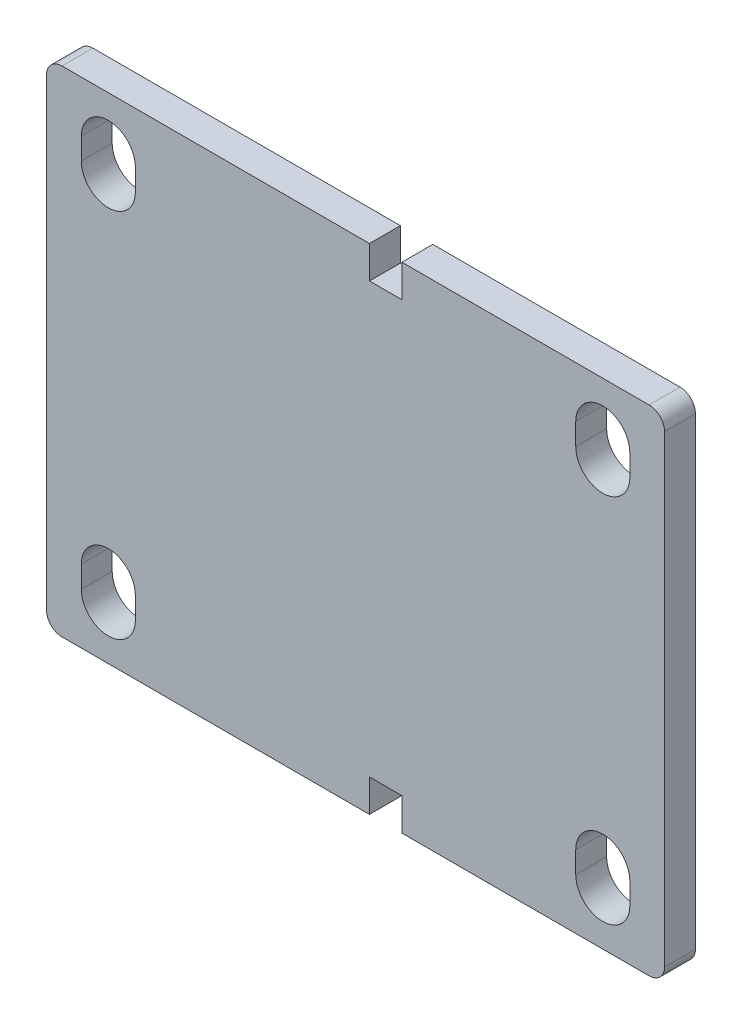
SolidWorks part; units mm, degrees
material "Acier S235"
ref_plane "Plan de face" through (0, 0, 0) normal (0, 0, 1) x (1, 0, 0)
ref_plane "Plan de dessus" through (0, 0, 0) normal (0, 1, 0) x (1, 0, 0)
ref_plane "Plan de droite" through (0, 0, 0) normal (1, 0, 0) x (0, 0, -1)
sketch "Esquisse1" plane through (0, 0, 0) normal (0, 0, 1) x (1, 0, 0)
  line L1 (100, -80) -> (-100, -80)
  line L2 (100, -80) -> (100, 80)
  line L3 (100, 80) -> (-100, 80)
  line L4 (-100, -80) -> (-100, 80)
  line L7 (-80, 60) -> (80, 60) construction
  line L8 (-80, 60) -> (-80, -60) construction
  line L9 (-80, -60) -> (80, -60) construction
  line L10 (80, 60) -> (80, -60) construction
  circle A0 centre (-80, 60) radius 8.75
  circle A1 centre (80, 60) radius 8.75
  circle A2 centre (80, -60) radius 8.75
  circle A3 centre (-80, -60) radius 8.75
  point P0 (0, 0)
extrude "Boss.-Extru.1" add sketch "Esquisse1" along normal blind 10
sketch "Esquisse2" plane through (0, 0, 10) normal (0, 0, 1) x (1, 0, 0)
  line L0 (100, 80) -> (-100, 80) construction
  line L1 (15, 80) -> (4.5, 80)
  line L2 (15, 80) -> (15, 69.5)
  line L3 (15, 69.5) -> (4.5, 69.5)
  line L4 (4.5, 80) -> (4.5, 69.5)
  line L5 (-100, -80) -> (100, -80) construction
  line L6 (15, -80) -> (4.5, -80)
  line L7 (15, -80) -> (15, -69.5)
  line L8 (15, -69.5) -> (4.5, -69.5)
  line L9 (4.5, -80) -> (4.5, -69.5)
  line L10 (100, -80) -> (100, 80) construction
  dimension "D1" = 10.5
  dimension "D2" = 85
  dimension "D3" = 10.5
extrude "Enlèv. mat.-Extru.1" cut sketch "Esquisse2" against normal blind 10
fillet "Congé1" radius 5 4 edges at (-100, -80, 5) (100, -80, 5) (100, 80, 5) (-100, 80, 5)
sketch "Esquisse3" plane through (0, 0, 10) normal (0, 0, 1) x (1, 0, 0)
  line L0 (-80, 63.5) -> (-80, 56.5) construction
  line L1 (-80, 60) -> (80, 60) construction
  line L2 (-80, 60) -> (-80, -60) construction
  line L3 (-80, -60) -> (80, -60) construction
  line L4 (80, 60) -> (80, -60) construction
  line L5 (-71.25, 63.5) -> (-71.25, 56.5)
  line L6 (-88.75, 63.5) -> (-88.75, 56.5)
  arc A0 (-71.25, 63.5) -> (-88.75, 63.5) centre (-80, 63.5) ccw
  arc A1 (-88.75, 56.5) -> (-71.25, 56.5) centre (-80, 56.5) ccw
  circle A2 centre (-80, 60) radius 8.75 construction
  point P8 (-80, 60)
  dimension "D1" = 7
extrude "Enlèv. mat.-Extru.2" cut sketch "Esquisse3" against normal through all
mirror "Symétrie1" about plane through (0, 0, 0) normal (0, 1, 0) of "Enlèv. mat.-Extru.2"
mirror "Symétrie2" about plane through (0, 0, 0) normal (1, 0, 0) of "Symétrie1", "Enlèv. mat.-Extru.2"
equation "\"D4@Esquisse1\"=\"D1@Esquisse1\""
equation "\"D5@Esquisse1\"=\"D1@Esquisse1\""
equation "\"D9@Esquisse1\"=\"D8@Esquisse1\"/2"
equation "\"D10@Esquisse1\"=\"D7@Esquisse1\"/2"
